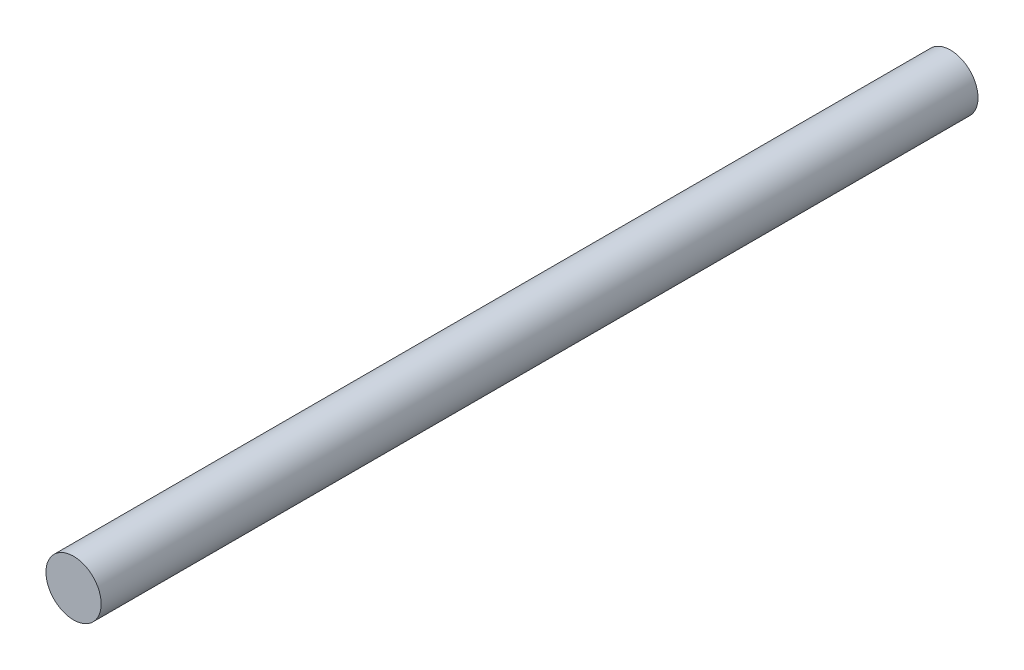
SolidWorks part; units mm, degrees
ref_plane "Front Plane" through (0, 0, 0) normal (0, 0, 1) x (1, 0, 0)
ref_plane "Top Plane" through (0, 0, 0) normal (0, 1, 0) x (1, 0, 0)
ref_plane "Right Plane" through (0, 0, 0) normal (1, 0, 0) x (0, 0, -1)
sketch "Sketch1" plane through (0, 0, 0) normal (0, 0, 1) x (1, 0, 0)
  circle A0 centre (0, 0) radius 2
  dimension "D1" = 4
extrude "Boss-Extrude1" add sketch "Sketch1" along normal blind 63.5
